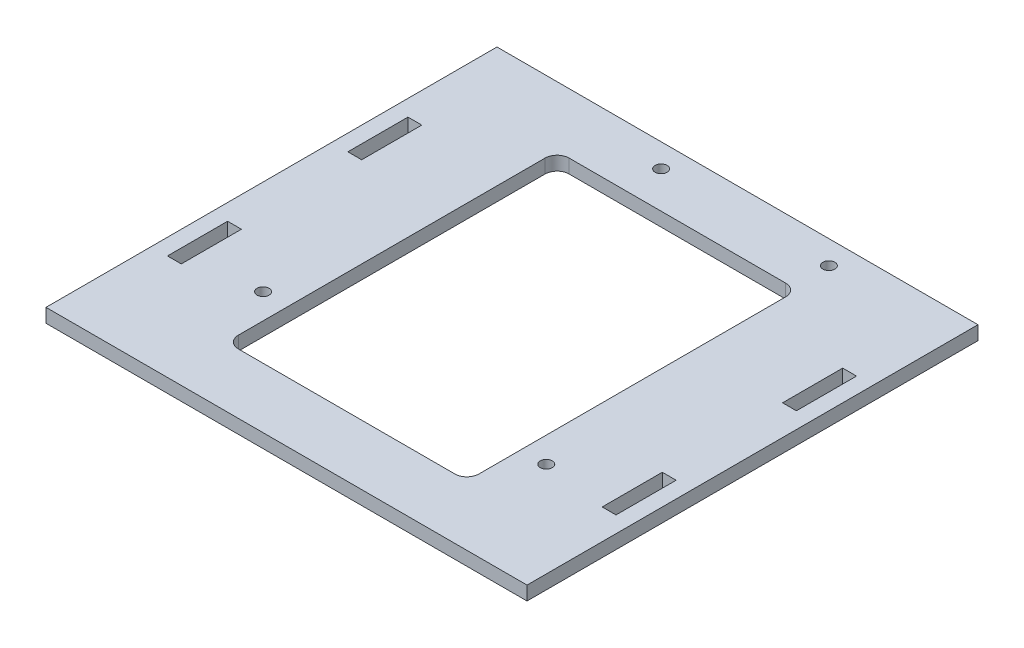
SolidWorks part; units mm, degrees
ref_plane "Front Plane" through (0, 0, 0) normal (0, 0, 1) x (1, 0, 0)
ref_plane "Top Plane" through (0, 0, 0) normal (0, 1, 0) x (1, 0, 0)
ref_plane "Right Plane" through (0, 0, 0) normal (1, 0, 0) x (0, 0, -1)
sketch "Sketch1" plane through (0, 0, 0) normal (0, 1, 0) x (1, 0, 0)
  line L0 (0, 0) -> (80, 0)
  line L1 (0, 0) -> (0, 75)
  line L2 (0, 75) -> (80, 75)
  line L3 (80, 75) -> (80, 0)
  dimension "D1" = 80
  dimension "D2" = 75
extrude "Boss-Extrude1" add sketch "Sketch1" along normal blind 2.3
sketch "Sketch2" plane through (0, 0, 0) normal (0, -1, 0) x (1, 0, 0)
  line L0 (40, -75) -> (5, -75) construction
  line L1 (80, -75) -> (0, -75) construction
  line L2 (40, -75) -> (75, -75) construction
  line L3 (5, -75) -> (2.7, -75) construction
  line L4 (75, -75) -> (77.3, -75) construction
  line L5 (5, -75) -> (5, 0) construction
  line L6 (0, 0) -> (80, 0) construction
  line L7 (2.7, -75) -> (2.7, 0) construction
  line L8 (75, -75) -> (75, 0) construction
  line L9 (77.3, -75) -> (77.3, 0) construction
  line L10 (40, -75) -> (40, -57.5) construction
  line L11 (40, -57.5) -> (2.7, -57.5) construction
  line L12 (40, -57.5) -> (77.3, -57.5) construction
  line L13 (2.7, -57.5) -> (2.7, -47.5)
  line L14 (2.7, -47.5) -> (2.7, -27.5) construction
  line L15 (2.7, -27.5) -> (2.7, -17.5)
  line L16 (2.7, -17.5) -> (5, -17.5)
  line L17 (5, -17.5) -> (5, -27.5)
  line L18 (5, -27.5) -> (2.7, -27.5)
  line L19 (2.7, -47.5) -> (5, -47.5)
  line L20 (5, -47.5) -> (5, -57.5)
  line L21 (5, -57.5) -> (2.7, -57.5)
  line L22 (77.3, -57.5) -> (77.3, -47.5)
  line L23 (77.3, -47.5) -> (77.3, -27.5) construction
  line L24 (77.3, -27.5) -> (77.3, -17.5)
  line L25 (77.3, -17.5) -> (75, -17.5)
  line L26 (75, -17.5) -> (75, -27.5)
  line L27 (75, -27.5) -> (77.3, -27.5)
  line L28 (77.3, -57.5) -> (75, -57.5)
  line L29 (75, -57.5) -> (75, -47.5)
  line L30 (75, -47.5) -> (77.3, -47.5)
  dimension "D1" = 35
  dimension "D2" = 35
  dimension "D3" = 2.3
  dimension "D4" = 2.3
  dimension "D5" = 17.5
  dimension "D6" = 10
  dimension "D7" = 20
  dimension "D8" = 10
  dimension "D9" = 10
  dimension "D10" = 20
  dimension "D11" = 10
extrude "Cut-Extrude1" cut sketch "Sketch2" against normal blind 10
sketch "Sketch3" plane through (0, 2.3, 0) normal (0, 1, 0) x (1, 0, 0)
  line L0 (40, 0) -> (40, 5) construction
  line L1 (0, 0) -> (80, 0) construction
  line L2 (40, 5) -> (13.3, 5) construction
  line L3 (40, 5) -> (66.7, 5) construction
  line L4 (13.3, 5) -> (13.3, 71.1) construction
  line L5 (13.3, 71.1) -> (66.7, 71.1) construction
  line L6 (66.7, 71.1) -> (66.7, 5) construction
  line L7 (13.3, 5) -> (15.8, 5) construction
  line L8 (66.7, 5) -> (64.2, 5) construction
  line L9 (15.8, 5) -> (15.8, 71.1) construction
  line L10 (64.2, 5) -> (64.2, 71.1) construction
  line L11 (13.3, 5) -> (13.3, 19) construction
  line L12 (13.3, 19) -> (66.7, 19) construction
  line L13 (13.3, 19) -> (13.3, 20.3) construction
  line L14 (13.3, 20.3) -> (66.7, 20.3) construction
  line L15 (64.2, 71.1) -> (59.1, 71.1) construction
  line L16 (59.1, 71.1) -> (31.2, 71.1) construction
  circle A0 centre (31.2, 71.1) radius 1
  circle A1 centre (59.1, 71.1) radius 1
  circle A2 centre (15.8, 20.3) radius 1
  circle A3 centre (64.2, 19) radius 1
  dimension "D11" = 2
  dimension "D1" = 5
  dimension "D2" = 26.7
  dimension "D3" = 26.7
  dimension "D4" = 66.1
  dimension "D5" = 2.5
  dimension "D6" = 2.5
  dimension "D7" = 14
  dimension "D8" = 1.3
  dimension "D9" = 5.1
  dimension "D10" = 27.9
extrude "Cut-Extrude2" cut sketch "Sketch3" against normal blind 10
sketch "Sketch4" plane through (0, 2.3, 0) normal (0, 1, 0) x (1, 0, 0)
  line L0 (40, 0) -> (40, 10) construction
  line L1 (0, 0) -> (80, 0) construction
  line L2 (40, 10) -> (20, 10)
  line L3 (40, 10) -> (60, 10) construction
  line L4 (60, 10) -> (60, 65)
  line L5 (60, 65) -> (20, 65)
  line L6 (20, 65) -> (20, 10)
  line L7 (40, 10) -> (60, 10)
  dimension "D1" = 10
  dimension "D2" = 20
  dimension "D3" = 20
  dimension "D4" = 55
extrude "Cut-Extrude3" cut sketch "Sketch4" against normal blind 10
fillet "Fillet1" radius 2 4 edges at (60, 1.15, -10) (20, 1.15, -10) (60, 1.15, -65) (20, 1.15, -65)
